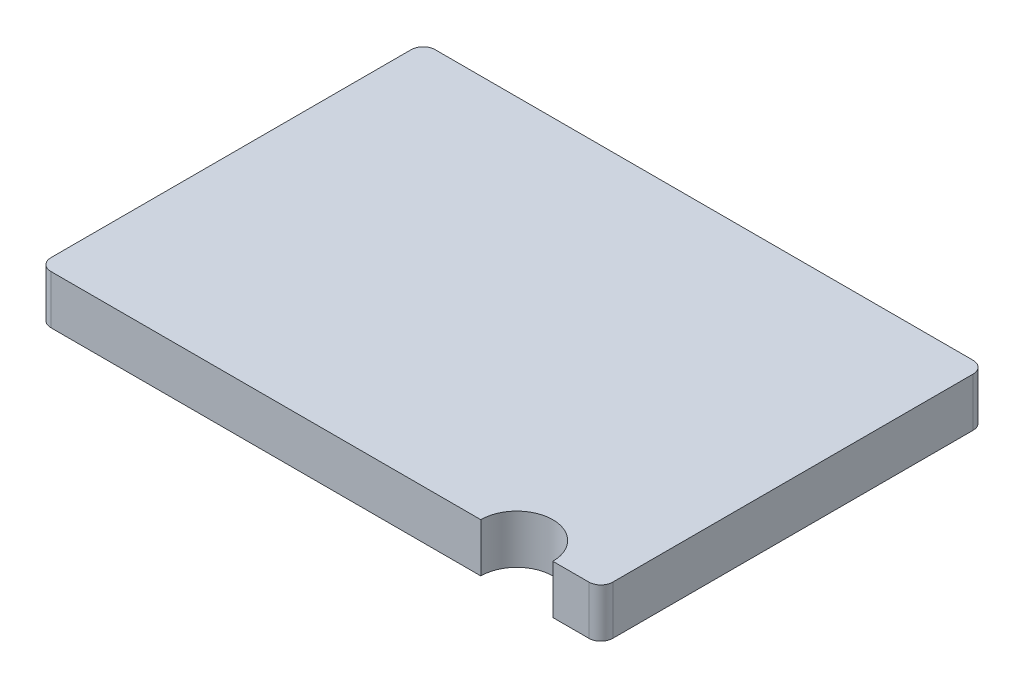
SolidWorks part; units mm, degrees
material "1060-H18"
ref_plane "Front Plane" through (0, 0, 0) normal (0, 0, 1) x (1, 0, 0)
ref_plane "Top Plane" through (0, 0, 0) normal (0, 1, 0) x (1, 0, 0)
ref_plane "Right Plane" through (0, 0, 0) normal (1, 0, 0) x (0, 0, -1)
sketch "Sketch1" plane through (0, 0, 0) normal (0, 1, 0) x (1, 0, 0)
  line L1 (-1.17, 0.8) -> (1.17, 0.8)
  line L2 (-1.17, 0.8) -> (-1.17, -0.8)
  line L3 (-1.17, -0.8) -> (1.17, -0.8)
  line L4 (1.17, 0.8) -> (1.17, -0.8)
  line L5 (-1.17, 0.8) -> (1.17, -0.8) construction
  line L6 (-1.17, -0.8) -> (1.17, 0.8) construction
  point P0 (0, 0)
  dimension "D1" = 2.34
  dimension "D2" = 1.6
extrude "Boss-Extrude1" add sketch "Sketch1" along normal blind 0.203
fillet "Fillet1" radius 0.05 4 edges at (-1.17, 0.1015, -0.8) (1.17, 0.1015, -0.8) (1.17, 0.1015, 0.8) (-1.17, 0.1015, 0.8)
sketch "Sketch2" plane through (0, 0.203, 0) normal (0, 1, 0) x (1, 0, 0)
  line L0 (-1.12, -0.8) -> (1.12, -0.8) construction
  line L1 (1.17, -0.75) -> (1.17, 0.75) construction
  circle A0 centre (0.82, -0.8) radius 0.15
  dimension "D1" = 0.3
  dimension "D2" = 0.35
extrude "Cut-Extrude1" cut sketch "Sketch2" against normal through all
